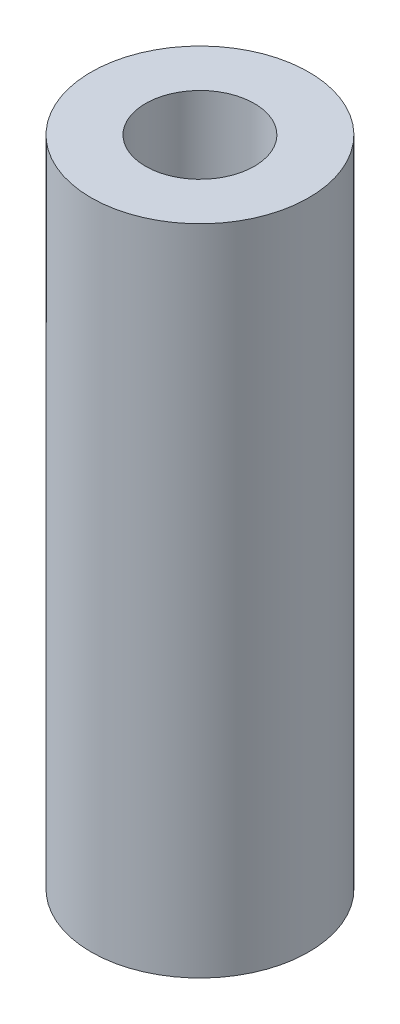
SolidWorks part; units mm, degrees
ref_plane "Front Plane" through (0, 0, 0) normal (0, 0, 1) x (1, 0, 0)
ref_plane "Top Plane" through (0, 0, 0) normal (0, 1, 0) x (1, 0, 0)
ref_plane "Right Plane" through (0, 0, 0) normal (1, 0, 0) x (0, 0, -1)
sketch "Sketch1" plane through (0, 0, 0) normal (0, 1, 0) x (1, 0, 0)
  circle A0 centre (0, 0) radius 2.5
  circle A1 centre (0, 0) radius 5
  dimension "D1" = 5
  dimension "D2" = 10
extrude "Boss-Extrude1" add sketch "Sketch1" along normal blind 30
